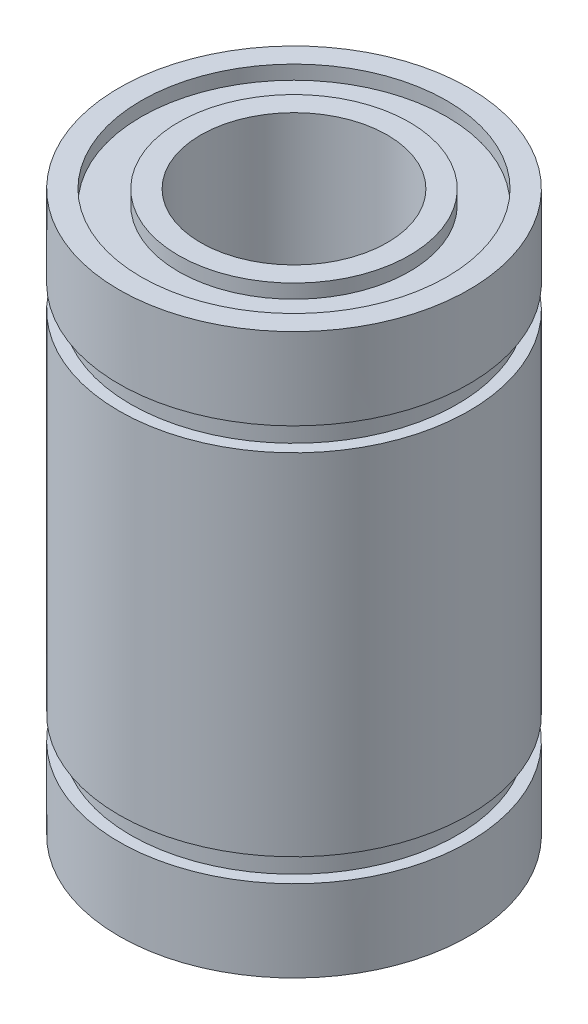
SolidWorks part; units mm, degrees
ref_plane "Plan de face" through (0, 0, 0) normal (0, 0, 1) x (1, 0, 0)
ref_plane "Plan de dessus" through (0, 0, 0) normal (0, 1, 0) x (1, 0, 0)
ref_plane "Plan de droite" through (0, 0, 0) normal (1, 0, 0) x (0, 0, -1)
sketch "Esquisse1" plane through (0, 0, 0) normal (0, 1, 0) x (1, 0, 0)
  circle A0 centre (0, 0) radius 7.5
  circle A1 centre (0, 0) radius 4
  dimension "D1" = 15
  dimension "D2" = 8
extrude "Boss.-Extru.1" add sketch "Esquisse1" along normal blind 12
ref_plane "Plan1" through (0, 4, 0) normal (0, -1, 0) x (-1, 0, 0)
sketch "Esquisse2" plane through (0, 4, 0) normal (0, -1, 0) x (-1, 0, 0)
  circle A0 centre (0, 0) radius 7.5
sketch "Esquisse4" plane through (0, 0, 0) normal (0, 0, 1) x (1, 0, 0)
  line L0 (-8.25, 4) -> (8.25, 4) construction
  line L1 (-8, 4.5) -> (-7, 4.5)
  line L2 (-8, 4.5) -> (-8, 3.5)
  line L3 (-8, 3.5) -> (-7, 3.5)
  line L4 (-7, 4.5) -> (-7, 3.5)
  line L5 (-8, 4.5) -> (-7, 3.5) construction
  line L6 (-8, 3.5) -> (-7, 4.5) construction
  line L7 (-7.5, 4) -> (7.5, 4) construction
  line L8 (-7.5, 12) -> (-7.5, 0) construction
  point P0 (-7.5, 4)
  dimension "D1" = 1
  dimension "D2" = 1
sweep "Enlèvement de matière-Balayage1" cut profiles "Esquisse4" path "Esquisse2"
sketch "Esquisse5" plane through (0, 0, 0) normal (0, -1, 0) x (-1, 0, 0)
  line L0 (0, 4) -> (0, 7.5) construction
  circle A0 centre (0, 0) radius 5.75
  circle A3 centre (0, 0) radius 4 construction
  circle A4 centre (0, 0) radius 7.5 construction
  point P10 (0, 5.75)
sketch "Esquisse6" plane through (0, 0, 0) normal (1, 0, 0) x (0, 0, -1)
  line L1 (6.55, 0.6) -> (4.95, 0.6)
  line L2 (6.55, 0.6) -> (6.55, -0.6)
  line L3 (6.55, -0.6) -> (4.95, -0.6)
  line L4 (4.95, 0.6) -> (4.95, -0.6)
  line L5 (6.55, 0.6) -> (4.95, -0.6) construction
  line L6 (6.55, -0.6) -> (4.95, 0.6) construction
  point P0 (5.75, 0)
  dimension "D1" = 1.6
  dimension "D2" = 1.2
sweep "Enlèvement de matière-Balayage2" cut profiles "Esquisse6" path "Esquisse5"
mirror "Symétrie1" about plane through (0, 12, 0) normal (0, 1, 0) of bodies 103
